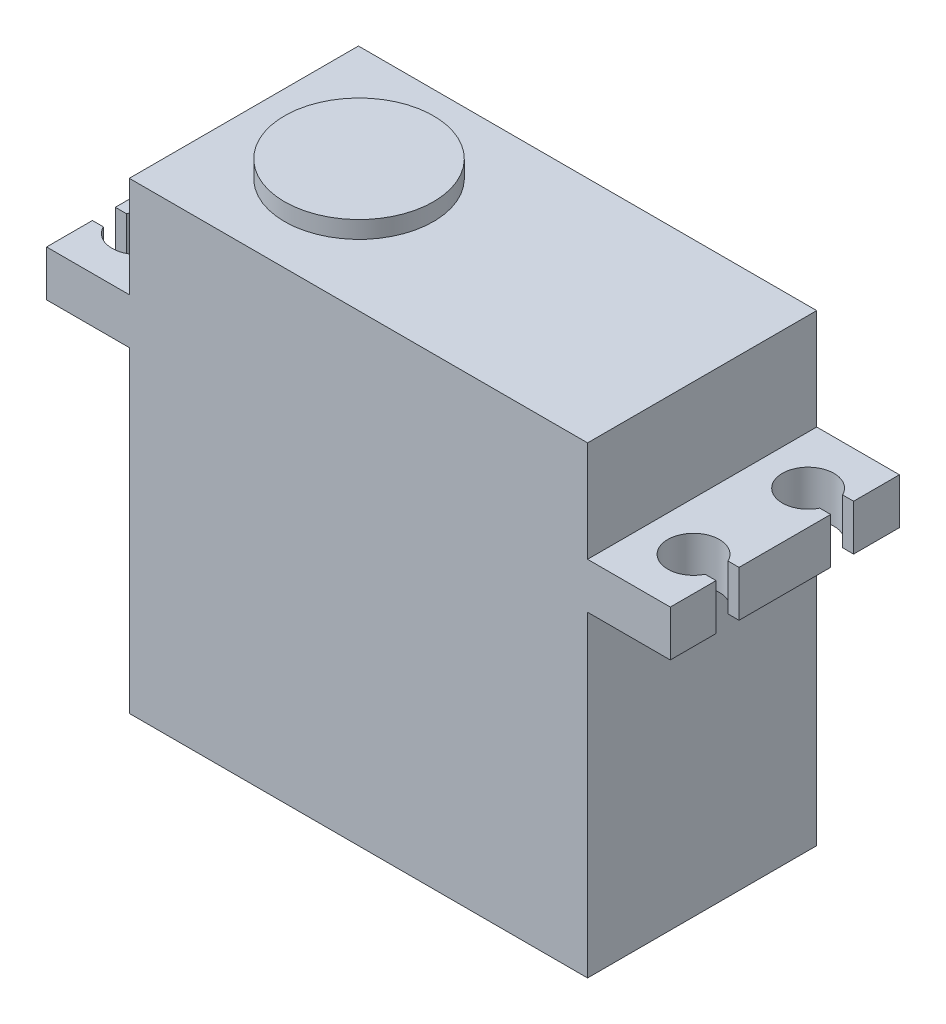
SolidWorks part; units mm, degrees
ref_plane "Front Plane" through (0, 0, 0) normal (0, 0, 1) x (1, 0, 0)
ref_plane "Top Plane" through (0, 0, 0) normal (0, 1, 0) x (1, 0, 0)
ref_plane "Right Plane" through (0, 0, 0) normal (1, 0, 0) x (0, 0, -1)
sketch "Sketch2" plane through (0, 0, 0) normal (0, 1, 0) x (1, 0, 0)
  line L1 (-20, -10) -> (20, -10)
  line L2 (-20, -10) -> (-20, 10)
  line L3 (-20, 10) -> (20, 10)
  line L4 (20, -10) -> (20, 10)
  line L5 (-20, -10) -> (20, 10) construction
  line L6 (-20, 10) -> (20, -10) construction
  point P0 (0, 0)
  dimension "D1" = 20
  dimension "D2" = 40
extrude "Boss-Extrude1" add sketch "Sketch2" along normal blind 27.65
sketch "Sketch3" plane through (-20, 0, 0) normal (-1, 0, 0) x (0, 0, 1)
  line L0 (0, 0) -> (0, 4) construction
  line L1 (-10, 0) -> (10, 0) construction
  line L3 (-3.5, 8) -> (3.5, 8)
  line L4 (-3.5, 8) -> (-3.5, 4)
  line L5 (-3.5, 4) -> (3.5, 4)
  line L6 (3.5, 8) -> (3.5, 4)
  line L7 (-3.5, 8) -> (3.5, 4) construction
  line L8 (-3.5, 4) -> (3.5, 8) construction
  point P4 (0, 6)
  dimension "D1" = 4
  dimension "D2" = 7
extrude "Boss-Extrude2" add sketch "Sketch3" along normal blind 5
sketch "Sketch5" plane through (0, 27.65, 0) normal (0, 1, 0) x (1, 0, 0)
  line L4 (20, -10) -> (20, 10)
  line L5 (20, 10) -> (-20, 10)
  line L6 (-20, 10) -> (-20, -10)
  line L7 (-20, -10) -> (20, -10)
  line L8 (20, -10) -> (20, 10)
  line L9 (20, 10) -> (-20, 10)
  line L10 (-20, 10) -> (-20, -10)
  line L11 (-20, -10) -> (20, -10)
  dimension "D1" = 0
extrude "Boss-Extrude5" add sketch "Sketch5" along normal blind 12.8
sketch "Sketch7" plane through (-20, 0, 0) normal (-1, 0, 0) x (0, 0, 1)
  line L0 (-10, 27.65) -> (10, 27.65)
  line L1 (10, 27.65) -> (10, 31.65)
  line L2 (10, 40.45) -> (10, 0) construction
  line L3 (-10, 31.65) -> (-10, 27.65)
  line L4 (-10, 40.45) -> (-10, 0) construction
  line L5 (10, 31.65) -> (-10, 31.65)
  dimension "D1" = 4
extrude "Boss-Extrude6" add sketch "Sketch7" along normal blind 7.22
sketch "Sketch8" plane through (0, 31.65, 0) normal (0, 1, 0) x (1, 0, 0)
  line L0 (-20, 10) -> (-20, 0) construction
  line L1 (-20, 0) -> (-27.22, 0) construction
  line L2 (-27.22, -10) -> (-27.22, 10) construction
  line L3 (-20, 5) -> (-27.22, 5) construction
  line L4 (-26.2656, 6) -> (-27.22, 6)
  line L8 (-27.22, 6) -> (-27.22, 4)
  line L9 (-27.22, 4) -> (-26.2656, 4)
  arc A1 (-26.2656, 4) -> (-26.2656, 6) centre (-24.25, 5) ccw
  dimension "D1" = 4.25
  dimension "D3" = 4.5
  dimension "D2" = 1
extrude "Cut-Extrude3" cut sketch "Sketch8" against normal blind 4
mirror "Mirror10" about plane through (0, 0, 0) normal (0, 0, 1) of "Cut-Extrude3"
mirror "Mirror11" about plane through (0, 0, 0) normal (1, 0, 0) of "Mirror10", "Cut-Extrude3", "Boss-Extrude6"
sketch "Sketch9" plane through (0, 40.45, 0) normal (0, 1, 0) x (1, 0, 0)
  line L0 (20, 0) -> (-20, 0) construction
  line L1 (20, -10) -> (20, 10) construction
  line L2 (-20, 10) -> (-20, -10) construction
  line L5 (-9.95, 0) -> (-9.95, 8.0914) construction
  circle A1 centre (-9.95, 0) radius 6.5
  circle A2 centre (-9.95, 0) radius 3
  dimension "D1" = 13
  dimension "D3" = 6
  dimension "D2" = 29.95
extrude "Boss-Extrude8" add sketch "Sketch9" along normal blind 1.5 contours A1 A2
sketch "Sketch10" plane through (0, 31.65, 0) normal (0, 1, 0) x (1, 0, 0)
  circle A0 centre (24, 5) radius 2 construction
  circle A1 centre (24, -5) radius 2 construction
  circle A2 centre (-24, 5) radius 2 construction
  circle A3 centre (-24, -5) radius 2 construction
